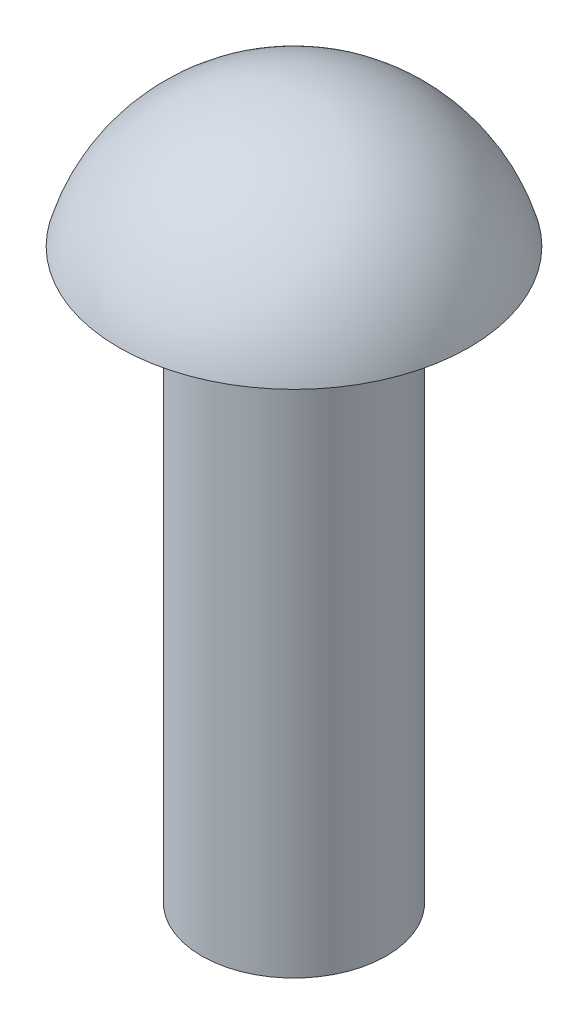
SolidWorks part; units mm, degrees
material "1060 Alloy"
ref_plane "Front Plane" through (0, 0, 0) normal (0, 0, 1) x (1, 0, 0)
ref_plane "Top Plane" through (0, 0, 0) normal (0, 1, 0) x (1, 0, 0)
ref_plane "Right Plane" through (0, 0, 0) normal (1, 0, 0) x (0, 0, -1)
sketch "Sketch1" plane through (0, 0, 0) normal (1, 0, 0) x (0, 0, -1)
  line L0 (0, 0) -> (0, -7.4) construction
  line L1 (0, -7.4) -> (0.975, -7.4)
  line L2 (0.975, -7.4) -> (0.975, -1.4)
  line L3 (0.975, -1.4) -> (1.85, -1.4)
  line L6 (0, 0) -> (0, -7.4)
  arc A0 (1.85, -1.4) -> (0, 0) centre (0, -1.9223) ccw
  dimension "D4" = 1.85
  dimension "D1" = 1.95
  dimension "D2" = 6
  dimension "D3" = 1.4
revolve "Revolve2" add sketch "Sketch1" angle 360 about L0
